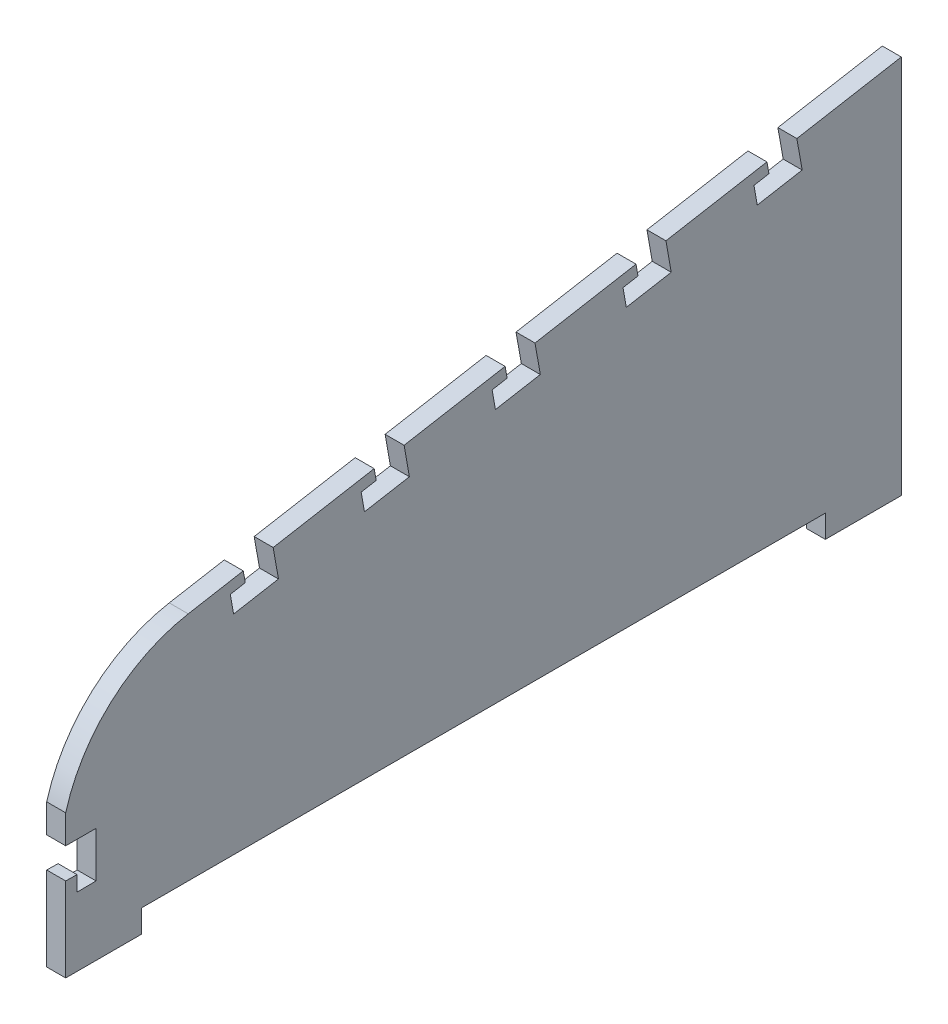
SolidWorks part; units mm, degrees
material "Maple"
ref_plane "Front Plane" through (0, 0, 0) normal (0, 0, 1) x (1, 0, 0)
ref_plane "Top Plane" through (0, 0, 0) normal (0, 1, 0) x (1, 0, 0)
ref_plane "Right Plane" through (0, 0, 0) normal (1, 0, 0) x (0, 0, -1)
sketch "Sketch1" plane through (0, 0, 0) normal (1, 0, 0) x (0, 0, -1)
  line L0 (-110, -6) -> (-90, -6)
  line L1 (-97.8341, 10.4125) -> (102.1659, 10.4125) construction
  line L2 (-97.8341, 10.4125) -> (-97.8341, 5.4125) construction
  line L3 (-97.8341, 5.4125) -> (102.1659, 5.4125) construction
  line L4 (102.1659, 10.4125) -> (102.1659, 5.4125) construction
  line L5 (-90, -6) -> (-90, 0)
  line L6 (-90, 0) -> (90, 0)
  line L7 (90, 0) -> (90, -6)
  line L8 (90, -6) -> (110, -6)
  line L9 (110, -6) -> (110, 94)
  line L10 (110, 94) -> (82.5046, 89.1518)
  line L11 (-110, 31.667) -> (-110, 24.131)
  line L12 (82.5046, 89.1518) -> (83.8938, 81.2734)
  line L13 (83.8938, 81.2734) -> (72.0761, 79.1896)
  line L14 (72.0761, 79.1896) -> (71.2079, 84.1136)
  line L15 (71.2079, 84.1136) -> (75.1471, 84.8082)
  line L16 (75.1471, 84.8082) -> (74.6262, 87.7626)
  line L17 (48.0364, 83.0741) -> (49.4255, 75.1957)
  line L18 (49.4255, 75.1957) -> (37.6078, 73.1119)
  line L19 (37.6078, 73.1119) -> (36.7396, 78.0359)
  line L20 (36.7396, 78.0359) -> (40.6788, 78.7305)
  line L21 (40.6788, 78.7305) -> (40.1579, 81.685)
  line L22 (13.5681, 76.9965) -> (14.9573, 69.118)
  line L23 (14.9573, 69.118) -> (3.1396, 67.0342)
  line L24 (3.1396, 67.0342) -> (2.2713, 71.9582)
  line L25 (2.2713, 71.9582) -> (6.2106, 72.6528)
  line L26 (6.2106, 72.6528) -> (5.6896, 75.6073)
  line L27 (-20.9002, 70.9188) -> (-19.511, 63.0403)
  line L28 (-19.511, 63.0403) -> (-31.3287, 60.9565)
  line L29 (-31.3287, 60.9565) -> (-32.1969, 65.8806)
  line L30 (-32.1969, 65.8806) -> (-28.2577, 66.5752)
  line L31 (-28.2577, 66.5752) -> (-28.7787, 69.5296)
  line L32 (-55.3685, 64.8411) -> (-53.9793, 56.9626)
  line L33 (-53.9793, 56.9626) -> (-65.797, 54.8788)
  line L34 (-65.797, 54.8788) -> (-66.6652, 59.8029)
  line L35 (-66.6652, 59.8029) -> (-62.726, 60.4975)
  line L36 (-62.726, 60.4975) -> (-63.2469, 63.4519)
  line L37 (74.6262, 87.7626) -> (48.0364, 83.0741) construction
  line L38 (74.6262, 87.7626) -> (48.0364, 83.0741)
  line L39 (40.1579, 81.685) -> (13.5681, 76.9965)
  line L40 (5.6896, 75.6073) -> (-20.9002, 70.9188)
  line L41 (-28.7787, 69.5296) -> (-55.3685, 64.8411)
  line L42 (-63.2469, 63.4519) -> (-77.7358, 60.8971)
  line L43 (-110, 24.131) -> (-102, 24.131)
  line L44 (-102, 24.131) -> (-102, 12.131)
  line L45 (-102, 12.131) -> (-106.9997, 12.0771)
  line L46 (-106.9997, 12.0771) -> (-107.0005, 16.0771)
  line L47 (-107.0005, 16.0771) -> (-110, 16.131)
  line L48 (-110, 16.131) -> (-110, -6)
  arc A0 (-77.7358, 60.8971) -> (-110, 31.667) centre (-70.6375, 20.6403) ccw
  point P4 (11.5169, -12.7528)
  dimension "D1" = 200
  dimension "D2" = 5
  dimension "D3" = 8
  dimension "D4" = 5
  dimension "D5" = 3
  dimension "D6" = 8
  dimension "D7" = 4
  dimension "D9" = 12
  dimension "D10" = 5
  dimension "D11" = 4
  dimension "D12" = 3
  dimension "D13" = 220
  dimension "D14" = 180
  dimension "D15" = 6
  dimension "D16" = 100
  dimension "D17" = 90
  dimension "D8" = 5
extrude "Boss-Extrude1" add sketch "Sketch1" along normal blind 5
